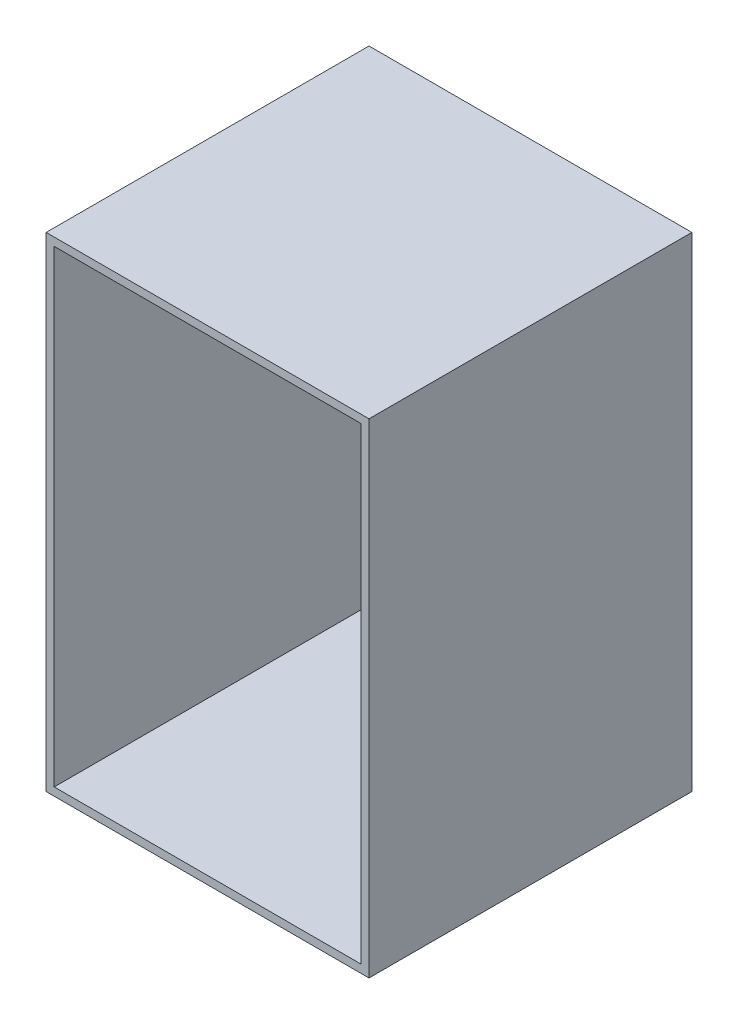
SolidWorks part; units mm, degrees
ref_plane "Front Plane" through (0, 0, 0) normal (0, 0, 1) x (1, 0, 0)
ref_plane "Top Plane" through (0, 0, 0) normal (0, 1, 0) x (1, 0, 0)
ref_plane "Right Plane" through (0, 0, 0) normal (1, 0, 0) x (0, 0, -1)
sketch "Sketch1" plane through (0, 0, 0) normal (0, 1, 0) x (1, 0, 0)
  line L6 (-60, -60) -> (60, -60)
  line L7 (-60, -60) -> (-60, 60)
  line L8 (-60, 60) -> (60, 60)
  line L9 (60, -60) -> (60, 60)
  line L10 (-60, -60) -> (60, 60) construction
  line L11 (-60, 60) -> (60, -60) construction
  point P0 (0, 0)
  dimension "D1" = 120
  dimension "D2" = 120
extrude "Boss-Extrude1" add sketch "Sketch1" along normal blind 180
shell "Shell1" thickness 3
